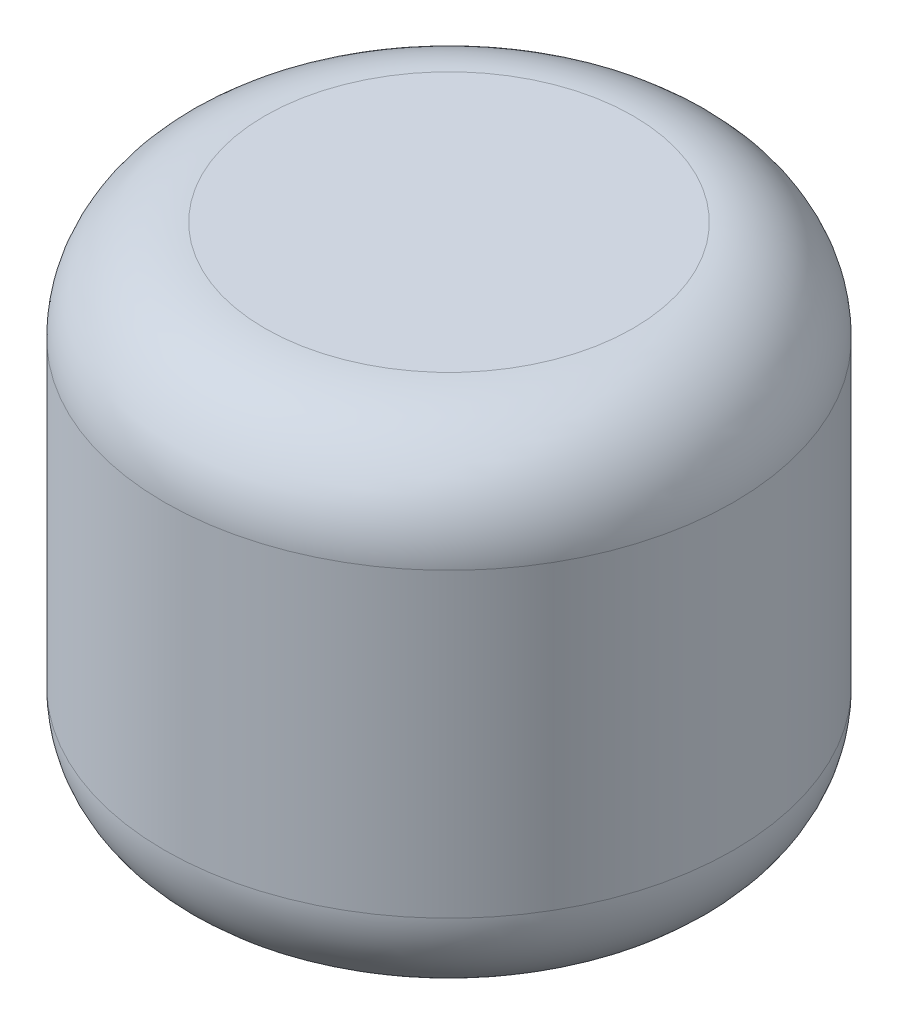
SolidWorks part; units mm, degrees
ref_plane "Спереди" through (0, 0, 0) normal (0, 0, 1) x (1, 0, 0)
ref_plane "Сверху" through (0, 0, 0) normal (0, 1, 0) x (1, 0, 0)
ref_plane "Справа" through (0, 0, 0) normal (1, 0, 0) x (0, 0, -1)
sketch "Эскиз1" plane through (0, 0, 0) normal (0, 1, 0) x (1, 0, 0)
  circle A0 centre (0, 0) radius 8.5
  dimension "D1" = 17
extrude "Бобышка-Вытянуть1" add sketch "Эскиз1" along normal blind 15
sketch "Эскиз2" plane through (0, 0, 0) normal (0, -1, 0) x (1, 0, 0)
  circle A0 centre (0, 0) radius 3.5
  dimension "D1" = 7
extrude "Вырез-Вытянуть1" cut sketch "Эскиз2" against normal blind 10
fillet "Скругление1" radius 3 2 edges at (0, 0, 8.5) (0, 15, 8.5)
